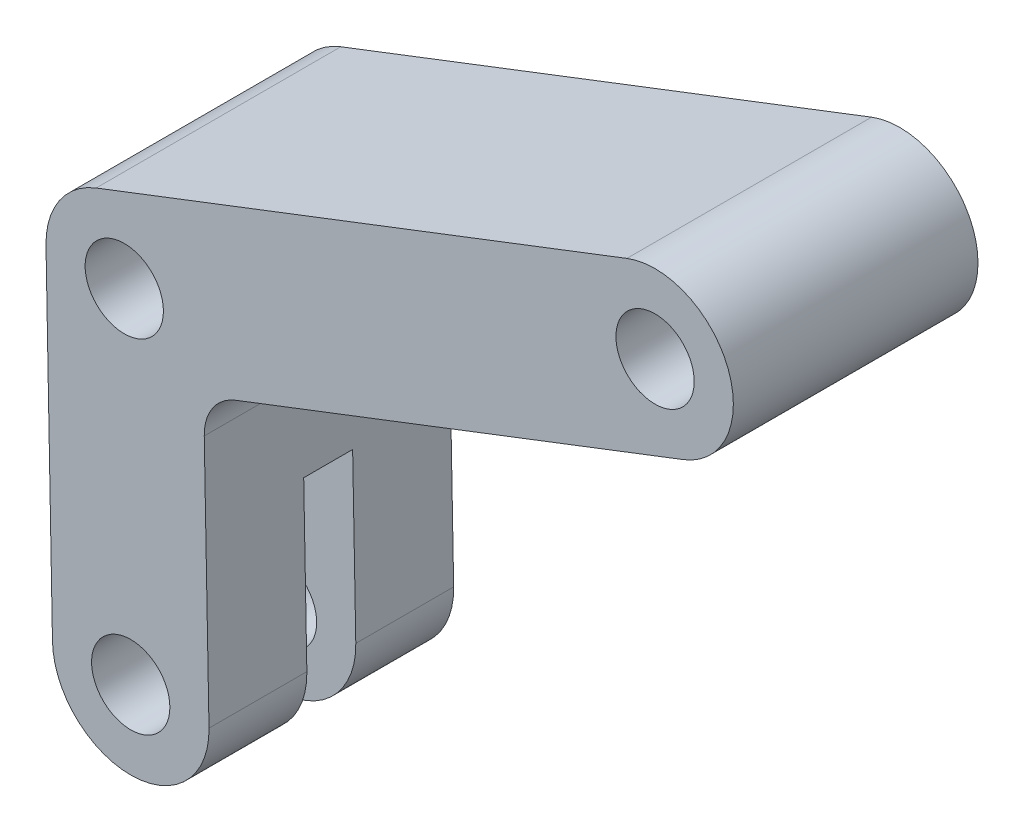
SolidWorks part; units mm, degrees
ref_plane "Front Plane" through (0, 0, 0) normal (0, 0, 1) x (1, 0, 0)
ref_plane "Top Plane" through (0, 0, 0) normal (0, 1, 0) x (1, 0, 0)
ref_plane "Right Plane" through (0, 0, 0) normal (1, 0, 0) x (0, 0, -1)
sketch "Sketch1" plane through (0, 0, 0) normal (0, 0, 1) x (1, 0, 0)
  line L0 (50.7048, 63.0755) -> (-3.5352, 42.1855)
  line L1 (56.4552, 48.1445) -> (7.4451, 29.2688)
  line L2 (-8, 0) -> (-8.6585, 34.5676)
  line L3 (8.0014, 0) -> (7.4451, 29.2688)
  circle A0 centre (0, 0) radius 4
  circle A1 centre (-0.66, 34.72) radius 4
  circle A2 centre (53.58, 55.61) radius 4
  arc A3 (-8, 0) -> (7.9986, 0.152) centre (0, 0) ccw
  arc A4 (-3.5352, 42.1855) -> (-8.6585, 34.5676) centre (-0.66, 34.72) ccw
  arc A5 (56.4552, 48.1445) -> (50.7048, 63.0755) centre (53.58, 55.61) ccw
  dimension "D1" = 8
  dimension "D2" = 8
  dimension "D3" = 8
  dimension "D5" = 34.72
  dimension "D6" = 53.58
  dimension "D7" = 55.61
  dimension "D8" = 16
  dimension "D9" = 16
  dimension "D10" = 16
  dimension "D4" = 0.66
extrude "Boss-Extrude1" add sketch "Sketch1" against normal blind 25 contours L1 A5 L0 A4 L2 A3 L3 A0 A1 A2
fillet "Fillet1" radius 5 1 edges at (7.4451, 29.2688, -12.5)
sketch "Sketch2" plane through (-7.9971, -0.1524, 0) normal (-0.9998, -0.019, 0) x (0, 0, 1)
  line L0 (0, -8) -> (0, 0.1524) construction
  line L1 (-15, 17) -> (-10, 17)
  line L2 (-15, 17) -> (-15, -13)
  line L3 (-15, -13) -> (-10, -13)
  line L4 (-10, 17) -> (-10, -13)
  line L5 (-25, -8) -> (0, -8) construction
  dimension "D1" = 5
  dimension "D2" = 10
  dimension "D3" = 25
  dimension "D4" = 30
extrude "Cut-Extrude1" cut sketch "Sketch2" against normal through all both and the other way through all
